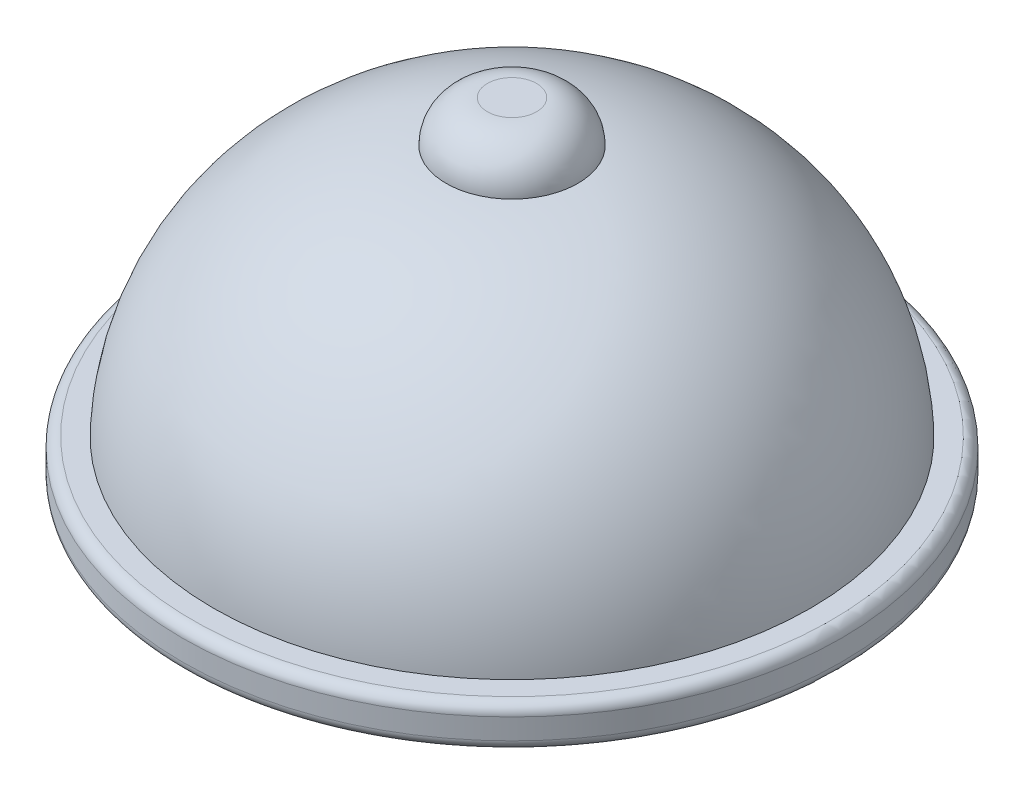
SolidWorks part; units mm, degrees
ref_plane "Front Plane" through (0, 0, 0) normal (0, 0, 1) x (1, 0, 0)
ref_plane "Top Plane" through (0, 0, 0) normal (0, 1, 0) x (1, 0, 0)
ref_plane "Right Plane" through (0, 0, 0) normal (1, 0, 0) x (0, 0, -1)
sketch "Sketch1" plane through (0, 0, 0) normal (0, 0, 1) x (1, 0, 0)
  line L0 (-183.2971, -161.2118) -> (-167.5266, -161.2118)
  line L1 (0, 0) -> (-40.4894, 0)
  line L2 (0, 0) -> (0, 44.2058)
  line L3 (0, 44.2058) -> (-15.0894, 44.2058)
  line L5 (-183.2971, -135.8118) -> (-196.0406, -135.8118)
  line L7 (-183.2971, -161.2118) -> (-196.0406, -161.2118)
  line L8 (-202.3906, -142.1618) -> (-202.3906, -154.8618)
  line L9 (-161.1766, -154.8618) -> (-161.1766, -135.8118)
  arc A0 (-15.0894, 44.2058) -> (-40.4894, 18.8058) centre (-15.0894, 18.8058) ccw
  arc A1 (-40.4894, 18.8058) -> (-183.2971, -135.8118) centre (-20.5699, -142.8509) ccw
  arc A2 (-40.4894, 0) -> (-161.1766, -135.8118) centre (-25.2861, -135.0396) ccw
  arc A3 (-196.0406, -161.2118) -> (-202.3906, -154.8618) centre (-196.0406, -154.8618) cw
  arc A4 (-196.0406, -135.8118) -> (-202.3906, -142.1618) centre (-196.0406, -142.1618) ccw
  arc A5 (-167.5266, -161.2118) -> (-161.1766, -154.8618) centre (-167.5266, -154.8618) ccw
  point P17 (-202.3906, -161.2118)
  point P20 (-202.3906, -135.8118)
  dimension "D1" = 25.4
  dimension "D3" = 6.35
  dimension "D4" = 6.35
  dimension "D2" = 25.4
revolve "Revolve1" add sketch "Sketch1" angle 360 about L2
